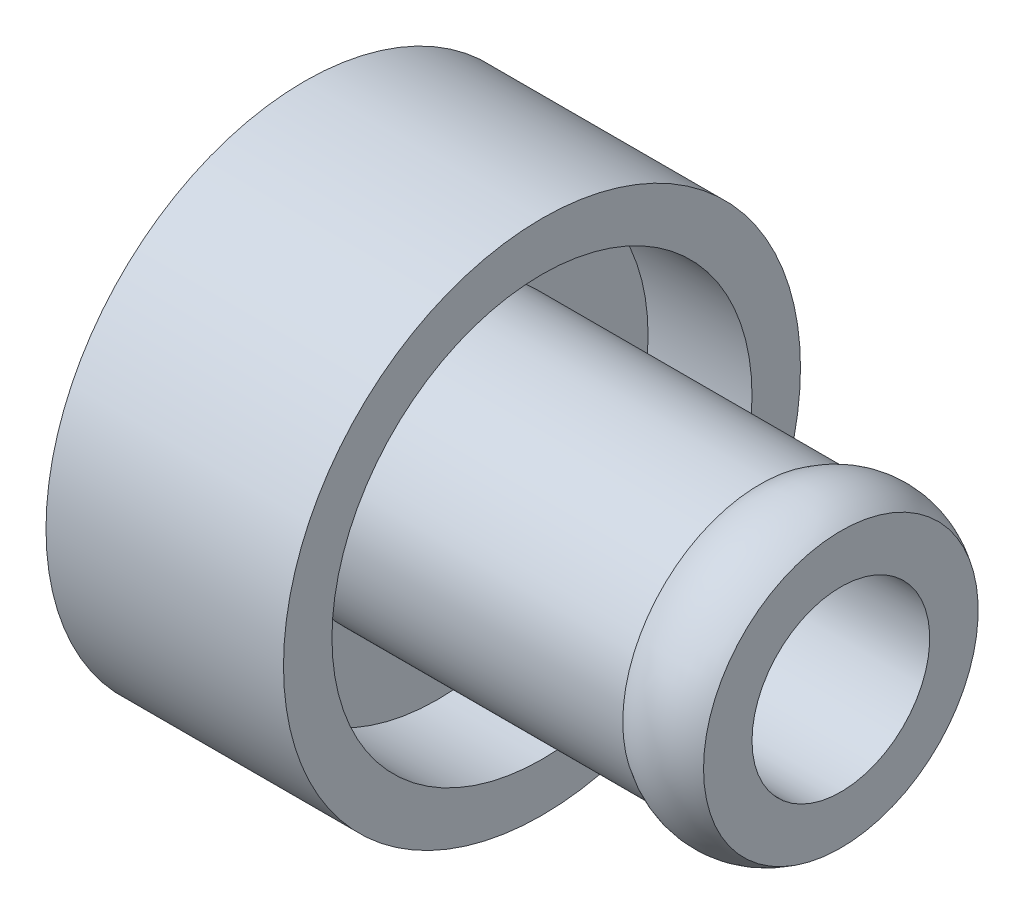
SolidWorks part; units mm, degrees
material "PE Low/Medium Density"
ref_plane "Front Plane" through (0, 0, 0) normal (0, 0, 1) x (1, 0, 0)
ref_plane "Top Plane" through (0, 0, 0) normal (0, 1, 0) x (1, 0, 0)
ref_plane "Right Plane" through (0, 0, 0) normal (1, 0, 0) x (0, 0, -1)
sketch "Sketch1" plane through (0, 0, 0) normal (0, 0, 1) x (1, 0, 0)
  line L0 (0, 0) -> (8.2819, 0) construction
  line L1 (0, 0) -> (0, 2.159)
  line L2 (0, 2.159) -> (1.338, 2.159)
  line L3 (1.338, 2.159) -> (1.338, 3.302)
  line L4 (1.338, 3.302) -> (0, 3.302)
  line L5 (0, 3.302) -> (0, 4.064)
  line L6 (0, 4.064) -> (3.7338, 4.064)
  line L7 (3.7338, 4.064) -> (3.7338, 3.302)
  line L8 (3.7338, 3.302) -> (2.1, 3.302)
  line L9 (2.1, 3.302) -> (2.1, 2.159)
  line L10 (2.1, 2.159) -> (8.4328, 2.159)
  line L11 (8.4328, 2.159) -> (8.4328, 0)
  line L12 (8.4328, 0) -> (0, 0)
  line L13 (-4.5329, 0) -> (14.6899, 0) construction
  dimension "D1" = 8.4328
  dimension "D2" = 8.128
  dimension "D3" = 4.318
  dimension "D4" = 0.762
  dimension "D6" = 0.762
  dimension "D7" = 4.699
revolve "Revolve1" add sketch "Sketch1" angle 360 about L0
sketch "Sketch2" plane through (0, 0, 0) normal (-1, 0, 0) x (0, 0, 1)
  circle A3 centre (0, 0) radius 1.397
  circle A4 centre (0, 0) radius 1.397
  dimension "D1" = 0.762
extrude "Cut-Extrude1" cut sketch "Sketch2" against normal through all
sketch "Sketch3" plane through (0, 0, 0) normal (0, 0, 1) x (1, 0, 0)
  line L0 (8.4328, 2.159) -> (2.1, 2.159) construction
  line L1 (8.4328, 2.159) -> (7.1628, 2.159)
  line L2 (0, 0) -> (10.8603, 0) construction
  line L3 (0, 4.064) -> (0, -4.064) construction
  arc A0 (8.4328, 2.159) -> (7.1628, 2.159) centre (7.7978, 1.2085) ccw
  dimension "D1" = 1.27
revolve "Revolve2" add sketch "Sketch3" angle 360 about L2
